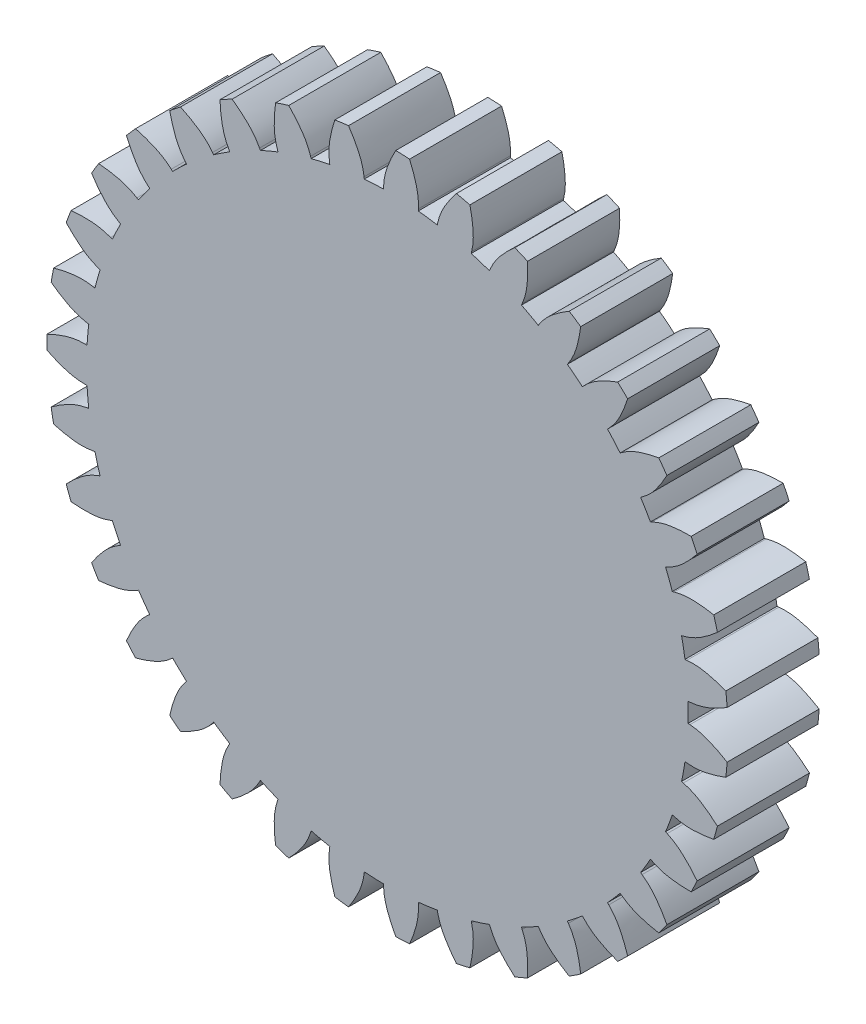
SolidWorks part; units mm, degrees
other "DetailItem2"
other "DetailItem5"
other "DetailItem6"
ref_plane "Front Plane" through (0, 0, 0) normal (0, 0, 1) x (1, 0, 0)
ref_plane "Top Plane" through (0, 0, 0) normal (0, 1, 0) x (1, 0, 0)
ref_plane "Right Plane" through (0, 0, 0) normal (1, 0, 0) x (0, 0, -1)
sketch "base_sketch" plane through (0, 0, 0) normal (0, 0, 1) x (1, 0, 0)
  line L0 (0, 0) -> (0, 17.5) construction
  line L1 (13.556, 17.5) -> (-17.4099, 17.5) construction
  line L2 (16.487, 11.4992) -> (-11.8716, 21.8209) construction
  line L3 (5.6244, 15.4529) -> (0, 0) construction
  line L4 (8.3345, 14.1761) -> (0, 0) construction
  line L5 (8.3345, 14.1761) -> (0.5887, 18.7301) construction
  line L6 (0, 0) -> (7.0086, 14.8763) construction
  line L7 (7.0086, 14.8763) -> (0.2371, 18.0665) construction
  line L8 (9.5912, 13.358) -> (1.0739, 19.4734) construction
  circle A0 centre (0, 0) radius 17.5 construction
  circle A1 centre (0, 0) radius 16.4446 construction
  arc A2 (5.6244, 15.4529) -> (7.0086, 14.8763) centre (0, 0) cw construction
  arc A3 (7.0086, 14.8763) -> (8.3345, 14.1761) centre (0, 0) cw construction
  arc A4 (8.3345, 14.1761) -> (9.5912, 13.358) centre (0, 0) cw
  circle A5 centre (0, 0) radius 18.5 construction
  dimension "D1" = 35
  dimension "D10" = 37
  dimension "D11" = 1.0554
  dimension "D2" = 20
  dimension "D3" = 5.9854
  dimension "D4" = 1.5
  dimension "D5" = 1.5
  dimension "D6" = 8.9854
  dimension "D7" = 7.4854
  dimension "D8" = 1.5
  dimension "D9" = 10.4854
sketch "tooth" plane through (0, 0, 0) normal (0, 0, 1) x (1, 0, 0)
  line L0 (0, 0) -> (1.3008, 28.9634) construction
  line L1 (0, 0) -> (0, 17.5) construction
  line L2 (-0.2088, 16.4433) -> (-0.2133, 16.3433)
  line L4 (1.6819, 16.3584) -> (1.6775, 16.2584)
  arc A0 (0.4553, 18.4944) -> (1.2044, 18.4608) centre (0, 0) cw
  circle A1 centre (0, 0) radius 18.5 construction
  circle A2 centre (0, 0) radius 16.4446 construction
  arc A3 (-0.2133, 16.3433) -> (1.6775, 16.2584) centre (0, 0) cw
  spline S0 degree 3 poles (-0.2088, 16.4433) (-0.195, 17.0206) (0.1796, 18.0761) (0.7543, 19.0299) (1.0739, 19.4734) knots 0 0 0 0 0.507907 1 1 1 1
  spline S1 degree 3 poles (1.6819, 16.3584) (1.72, 16.9346) (1.4415, 18.0194) (0.9546, 19.021) (0.676, 19.4913) knots 0 0 0 0 0.507907 1 1 1 1
  dimension "D1" = 2.571
  dimension "D3" = 0.1
sketch "Sketch12" plane through (0, 0, 0) normal (0, 0, 1) x (1, 0, 0)
  circle A0 centre (0, 0) radius 16.3447
  arc A1 (1.6775, 16.2584) -> (-0.2133, 16.3433) centre (0, 0) ccw construction
extrude "core_cyl" add sketch "Sketch12" along normal blind 5
extrude "tooth_ex" add sketch "tooth" along normal blind 5
ref_axis "Axis1" through (0, 0, 0) along (0, 0, 1)
pattern_circular "CirPattern1" count 35 over 360 about axis through (0, 0, 0) along (0, 0, 1) of "tooth_ex"
sketch "Sketch13" plane through (0, 0, 5) normal (0, 0, 1) x (1, 0, 0)
  circle A0 centre (0, 0) radius 12
  dimension "D1" = 24
equation "\"m\"= 1'module"
equation "\"P\"= 35'pitch diameter"
equation "\"N\"= \"P\" / \"m\"'number of teeth"
equation "\"D6@base_sketch\"=\"D5@base_sketch\"+\"D4@base_sketch\"+\"D3@base_sketch\""
equation "\"D7@base_sketch\"=\"D3@base_sketch\"+\"D4@base_sketch\""
equation "\"D1@tooth\"=360/\"N\"/4"
equation "\"D1@base_sketch\" = \"P\""
equation "\"D9@base_sketch\"=\"D6@base_sketch\"+\"D8@base_sketch\""
equation "\"D10@base_sketch\"=\"P\"+0*\"D11@base_sketch\"+2*\"m\""
